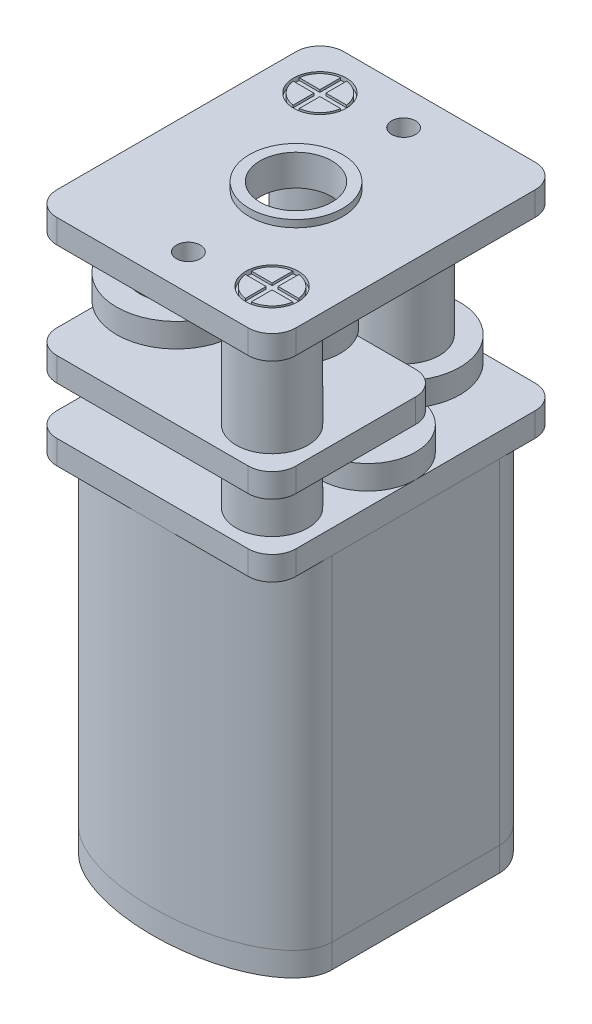
SolidWorks part; units mm, degrees
ref_plane "Alzado" through (0, 0, 0) normal (0, 0, 1) x (1, 0, 0)
ref_plane "Planta" through (0, 0, 0) normal (0, 1, 0) x (1, 0, 0)
ref_plane "Vista lateral" through (0, 0, 0) normal (1, 0, 0) x (0, 0, -1)
sketch "Croquis1" plane through (0, 0, 0) normal (0, 1, 0) x (1, 0, 0)
  line L0 (0, 0) -> (0, 3.5) construction
  line L1 (-5, -6) -> (5, -6) construction
  line L2 (-5, -6) -> (-5, 6) construction
  line L3 (-5, 6) -> (5, 6) construction
  line L4 (5, -6) -> (5, 6) construction
  line L5 (-5, -6) -> (5, 6) construction
  line L6 (-5, 6) -> (5, -6) construction
  line L7 (0, 0) -> (0, -3.5) construction
  line L8 (-5, 3.5) -> (0, 3.5) construction
  line L9 (0, 3.5) -> (5, 3.5) construction
  line L10 (-5, -3.5) -> (0, -3.5) construction
  line L11 (0, -3.5) -> (5, -3.5) construction
  line L12 (0, 0) -> (5, 0) construction
  line L13 (0, 0) -> (-5, 0) construction
  line L14 (5, 3.5) -> (5, -3.5)
  line L15 (-5, 3.5) -> (-5, -3.5)
  ellipse E0 centre (0, -3.5) end of major axis (5, -3.5) minor radius 2.5 (5, -3.5) -> (-5, -3.5) cw
  ellipse E1 centre (0, 3.5) end of major axis (-5, 3.5) minor radius 2.5 (5, 3.5) -> (-5, 3.5) ccw
  point P0 (0, 0)
  dimension "D1" = 12
  dimension "D2" = 10
extrude "Saliente-Extruir1" add sketch "Croquis1" along normal blind 1
sketch "Croquis2" plane through (0, 0, 0) normal (0, -1, 0) x (1, 0, 0)
  line L0 (-5, 3.5) -> (0, 3.5) construction
  line L1 (0, 3.5) -> (5, 3.5) construction
  line L2 (0, 0) -> (5, 0) construction
  line L3 (5, 3.5) -> (5, -3.5) construction
  line L4 (0, 0) -> (0, 3.5) construction
  line L5 (-5, -3.5) -> (0, -3.5) construction
  line L6 (0, -3.5) -> (5, -3.5) construction
  circle A0 centre (0, 0) radius 2.5
extrude "Saliente-Extruir2" add sketch "Croquis2" along normal blind 1
sketch "Croquis3" plane through (0, -1, 0) normal (0, -1, 0) x (1, 0, 0)
  circle A0 centre (0, 0) radius 1
extrude "Cortar-Extruir1" cut sketch "Croquis3" against normal blind 0.5
sketch "Croquis4" plane through (0, 0, 0) normal (0, -1, 0) x (1, 0, 0)
  line L0 (5, 3.5) -> (-5, 3.5) construction
  line L1 (-5, -3.5) -> (5, -3.5) construction
  line L2 (0, 0) -> (5, 0) construction
  line L4 (0, 0) -> (0, 3.5) construction
  line L5 (-0.75, 3.5) -> (0.75, 3.5)
  line L6 (0.75, 3.5) -> (0.75, 3.8)
  line L7 (-0.75, 3.5) -> (-0.75, 3.8)
  line L8 (-0.75, 3.8) -> (0.75, 3.8)
  line L9 (-0.75, -3.5) -> (-0.75, -3.8)
  line L10 (-0.75, -3.8) -> (0.75, -3.8)
  line L11 (0.75, -3.5) -> (0.75, -3.8)
  line L12 (-0.75, -3.5) -> (0.75, -3.5)
  line L13 (5, 3.5) -> (5, -3.5) construction
extrude "Saliente-Extruir3" add sketch "Croquis4" along normal blind 1.5
sketch "Croquis5" plane through (0, 0, -3.8) normal (0, 0, -1) x (-1, 0, 0)
  line L0 (0, -1.5) -> (0, 0) construction
  line L1 (0.75, -1.5) -> (-0.75, -1.5) construction
  line L2 (-0.75, -0.75) -> (0, -0.75) construction
  line L3 (-0.75, -1.5) -> (-0.75, 0) construction
  line L4 (0, -0.75) -> (0.75, -0.75) construction
  line L5 (0.75, -1.5) -> (0.75, 0) construction
  circle A0 centre (0, -0.75) radius 0.5
extrude "Cortar-Extruir2" cut sketch "Croquis5" against normal blind 0.3
sketch "Croquis6" plane through (0, 0, 3.8) normal (0, 0, 1) x (1, 0, 0)
  line L0 (0, -1.5) -> (0, 0) construction
  line L1 (0.75, -1.5) -> (-0.75, -1.5) construction
  line L2 (0.75, 0) -> (-0.75, 0) construction
  line L3 (0, -0.75) -> (0.75, -0.75) construction
  line L4 (0.75, -1.5) -> (0.75, 0) construction
  line L5 (0, -0.75) -> (-0.75, -0.75) construction
  line L6 (-0.75, -1.5) -> (-0.75, 0) construction
  circle A0 centre (0, -0.75) radius 0.5
extrude "Cortar-Extruir3" cut sketch "Croquis6" against normal blind 0.3
sketch "Croquis7" plane through (0, 1, 0) normal (0, 1, 0) x (1, 0, 0)
  line L2 (-5, 3.5) -> (-5, -3.5)
  line L3 (5, -3.5) -> (5, 3.5)
  line L4 (-5, 3.5) -> (-5, -3.5)
  line L5 (5, -3.5) -> (5, 3.5)
  ellipse E2 centre (0, 3.5) end of major axis (-5, 3.5) minor radius 2.5 (5, 3.5) -> (-5, 3.5) ccw
  ellipse E3 centre (0, -3.5) end of major axis (-5, -3.5) minor radius 2.5 (-5, -3.5) -> (5, -3.5) ccw
  ellipse E4 centre (0, 3.5) end of major axis (-5, 3.5) minor radius 2.5 (5, 3.5) -> (-5, 3.5) ccw
  ellipse E5 centre (0, -3.5) end of major axis (-5, -3.5) minor radius 2.5 (-5, -3.5) -> (5, -3.5) ccw
  dimension "D1" = 0
extrude "Saliente-Extruir4" add sketch "Croquis7" along normal blind 14 separate body
sketch "Croquis8" plane through (0, 15, 0) normal (0, 1, 0) x (1, 0, 0)
  line L1 (-5, 6) -> (5, 6)
  line L2 (5, 6) -> (5, -6)
  line L3 (5, -6) -> (-5, -6)
  line L4 (-5, -6) -> (-5, 6)
extrude "Saliente-Extruir5" add sketch "Croquis8" along normal blind 1 separate body
sketch "Croquis23" plane through (0, 16, 0) normal (0, 1, 0) x (1, 0, 0)
  line L0 (5, 6) -> (5, 1) construction
  line L1 (5, -6) -> (5, 6) construction
  line L2 (5, 6) -> (0, 6) construction
  line L3 (5, 6) -> (-5, 6) construction
  line L4 (0, 6) -> (0, 1) construction
  line L5 (0, 1) -> (5, 1) construction
  circle A0 centre (0, 0) radius 1
extrude "Saliente-Extruir13" add sketch "Croquis23" along normal blind 1 separate body
sketch "Croquis25" plane through (0, 16, 0) normal (0, 1, 0) x (1, 0, 0)
  line L0 (1, 0) -> (5, 0) construction
  line L1 (5, -6) -> (5, 6) construction
  circle A0 centre (0, 0) radius 1 construction
  circle A1 centre (3, 0) radius 2
extrude "Saliente-Extruir18" add sketch "Croquis25" along normal blind 1 separate body
sketch "Croquis26" plane through (0, 17, 0) normal (0, 1, 0) x (1, 0, 0)
  circle A0 centre (3, 0) radius 1
extrude "Saliente-Extruir19" add sketch "Croquis26" along normal blind 1
sketch "Croquis27" plane through (0, 17, 0) normal (0, 1, 0) x (1, 0, 0)
  line L0 (3, 1) -> (5, 1) construction
  line L1 (5, -6) -> (5, 6) construction
  line L2 (5, 1) -> (5, 6) construction
  line L3 (5, 6) -> (0, 6) construction
  line L4 (5, 6) -> (-5, 6) construction
  line L5 (0, 6) -> (0, 1) construction
  line L6 (0, 1) -> (3, 1) construction
  line L7 (1, 3) -> (2, 3) construction
  line L8 (1, 1) -> (1, 2) construction
  line L9 (1, 2) -> (0, 2) construction
  line L10 (2, 3) -> (2, 2) construction
  circle A0 centre (3, 0) radius 1 construction
  circle A1 centre (3, 0) radius 1 construction
  circle A2 centre (1, 2) radius 1 construction
  circle A3 centre (1.5, 3) radius 2.3541
extrude "Saliente-Extruir21" add sketch "Croquis27" along normal blind 1 separate body
sketch "Croquis29" plane through (0, 18, 0) normal (0, 1, 0) x (1, 0, 0)
  circle A0 centre (1.5, 3) radius 1.5
extrude "Saliente-Extruir22" add sketch "Croquis29" along normal blind 3
fillet "Redondeo1" radius 1 1 edges at (-5, 15.5, -6)
fillet "Redondeo2" radius 1 1 edges at (5, 15.5, -6)
fillet "Redondeo3" radius 1 1 edges at (5, 15.5, 6)
fillet "Redondeo4" radius 1 1 edges at (-5, 15.5, 6)
sketch "Croquis9" plane through (0, 16, 0) normal (0, 1, 0) x (1, 0, 0)
  line L0 (-5, 6) -> (-1, 6) construction
  line L1 (-3, 2) -> (-3, 6) construction
  line L2 (4, 6) -> (-4, 6) construction
  line L3 (-1, 6) -> (-1, 2) construction
  line L4 (-1, 2) -> (-5, 2) construction
  line L5 (-5, 5) -> (-5, -5) construction
  line L6 (-5, 2) -> (-5, 6) construction
  line L7 (-5, 4) -> (-3, 4) construction
  line L8 (-3, 4) -> (-1, 4) construction
  line L9 (5, -6) -> (1, -6) construction
  line L10 (-4, -6) -> (4, -6) construction
  line L11 (1, -6) -> (1, -2) construction
  line L12 (1, -2) -> (5, -2) construction
  line L13 (5, -5) -> (5, 5) construction
  line L14 (5, -2) -> (5, -6) construction
  line L15 (3, -2) -> (3, -6) construction
  line L16 (1, -4) -> (3, -4) construction
  line L17 (3, -4) -> (5, -4) construction
  circle A0 centre (-3, 4) radius 1.5
  circle A1 centre (3, -4) radius 1.5
extrude "Saliente-Extruir6" add sketch "Croquis9" along normal blind 2
sketch "Croquis10" plane through (0, 18, 0) normal (0, 1, 0) x (1, 0, 0)
  line L0 (-3, 4) -> (-5, 4) construction
  line L1 (-5, 5) -> (-5, -5) construction
  line L2 (-3, 4) -> (-3, 6) construction
  line L3 (4, 6) -> (-4, 6) construction
  line L4 (-5, 6) -> (5, 6)
  line L5 (5, 6) -> (5, -6)
  line L6 (5, -6) -> (-5, -6)
  line L7 (-5, -6) -> (-5, 6)
extrude "Saliente-Extruir7" add sketch "Croquis10" along normal blind 1
sketch "Croquis11" plane through (0, 19, 0) normal (0, 1, 0) x (1, 0, 0)
  line L0 (5, -6) -> (3, -6) construction
  line L1 (-5, -6) -> (5, -6) construction
  line L2 (3, -6) -> (3, -4) construction
  line L3 (3, -4) -> (5, -4) construction
  line L4 (5, -6) -> (5, 6) construction
  line L5 (5, -4) -> (5, -6) construction
  line L6 (-5, 6) -> (-5, 4) construction
  line L7 (-5, 6) -> (-5, -6) construction
  line L8 (-5, 4) -> (-3, 4) construction
  line L9 (-3, 4) -> (-3, 6) construction
  line L10 (5, 6) -> (-5, 6) construction
  line L11 (-3, 6) -> (-5, 6) construction
  circle A0 centre (3, -4) radius 1.5
  circle A1 centre (-3, 4) radius 1.5
extrude "Saliente-Extruir8" add sketch "Croquis11" along normal blind 4
sketch "Croquis12" plane through (0, 19, 0) normal (0, 1, 0) x (1, 0, 0)
  line L0 (5, 6) -> (0, 6)
  line L1 (5, 6) -> (-5, 6) construction
  line L2 (0, 6) -> (0, 1)
  line L3 (0, 1) -> (5, 1)
  line L4 (5, -6) -> (5, 6) construction
  line L5 (5, 1) -> (5, 6)
extrude "Cortar-Extruir4" cut sketch "Croquis12" against normal blind 1
sketch "Croquis30" plane through (0, 19, 0) normal (0, 1, 0) x (1, 0, 0)
  circle A0 centre (0, 0) radius 1.8541
extrude "Saliente-Extruir24" add sketch "Croquis30" along normal blind 1 separate body
sketch "Croquis31" plane through (0, 20, 0) normal (0, 1, 0) x (1, 0, 0)
  circle A0 centre (0, 0) radius 1
extrude "Saliente-Extruir26" add sketch "Croquis31" along normal blind 1 separate body
sketch "Croquis32" plane through (0, 20, 0) normal (0, 1, 0) x (1, 0, 0)
  line L0 (0, 0) -> (0, -2) construction
  line L1 (0, -2) -> (-2, -2) construction
  line L2 (-2, -2) -> (-2, 0) construction
  line L3 (-2, 0) -> (-3, 0) construction
  line L4 (-3, 0) -> (-3, -3) construction
  line L5 (-3, -3) -> (0, -3) construction
  line L6 (0, -3) -> (0, -2) construction
  line L7 (-2.5, 0) -> (-2.5, -2.5) construction
  line L8 (-2.5, -2.5) -> (0, -2.5) construction
  circle A0 centre (0, 0) radius 2 construction
  circle A1 centre (-2.5, -2.5) radius 2.5
extrude "Saliente-Extruir27" add sketch "Croquis32" along normal blind 1 separate body
sketch "Croquis33" plane through (0, 21, 0) normal (0, 1, 0) x (1, 0, 0)
  circle A0 centre (0, 0) radius 2 construction
  circle A1 centre (-2.5, -2.5) radius 1.5355
extrude "Saliente-Extruir28" add sketch "Croquis33" along normal blind 2 separate body
sketch "Croquis34" plane through (0, 21, 0) normal (0, 1, 0) x (1, 0, 0)
  circle A0 centre (1.5, 3) radius 0.2
extrude "Saliente-Extruir29" add sketch "Croquis34" along normal blind 2 and the other way blind 5 separate body
sketch "Croquis35" plane through (0, 23, 0) normal (0, 1, 0) x (1, 0, 0)
  circle A0 centre (-2.5, -2.5) radius 0.2
extrude "Saliente-Extruir30" add sketch "Croquis35" against normal blind 4 separate body
sketch "Croquis36" plane through (0, 21, 0) normal (0, 1, 0) x (1, 0, 0)
  circle A0 centre (0, 0) radius 0.2
extrude "Saliente-Extruir31" add sketch "Croquis36" along normal blind 2 separate body
fillet "Redondeo5" radius 1 1 edges at (5, 18.5, -1)
fillet "Redondeo6" radius 1 1 edges at (0, 18.5, -6)
fillet "Redondeo7" radius 1 1 edges at (-5, 18.5, -6)
fillet "Redondeo8" radius 1 1 edges at (-5, 18.5, 6)
fillet "Redondeo9" radius 1 1 edges at (5, 18.5, 6)
sketch "Croquis13" plane through (0, 23, 0) normal (0, 1, 0) x (1, 0, 0)
  line L2 (-5, 6) -> (5, 6)
  line L3 (5, 6) -> (5, -6)
  line L4 (5, -6) -> (-5, -6)
  line L5 (-5, -6) -> (-5, 6)
extrude "Saliente-Extruir9" add sketch "Croquis13" along normal blind 1
sketch "Croquis14" plane through (0, 24, 0) normal (0, 1, 0) x (1, 0, 0)
  line L0 (0, 6) -> (0, 0) construction
  line L1 (5, 6) -> (-5, 6) construction
  line L2 (0, 0) -> (0, -6) construction
  line L3 (-5, -6) -> (5, -6) construction
  line L4 (-5, 0) -> (0, 0) construction
  line L5 (-5, 6) -> (-5, -6) construction
  line L6 (0, 0) -> (5, 0) construction
  circle A0 centre (0, 0) radius 1.95
  circle A1 centre (0, 0) radius 1.5
extrude "Saliente-Extruir10" add sketch "Croquis14" along normal blind 0.3
sketch "Croquis15" plane through (0, 24, 0) normal (0, 1, 0) x (1, 0, 0)
  line L0 (0, 0) -> (0, 4.5) construction
  line L1 (0, 0) -> (5, 0) construction
  circle A0 centre (0, 4.5) radius 0.5
  circle A1 centre (0, -4.5) radius 0.5
extrude "Cortar-Extruir5" cut sketch "Croquis15" against normal blind 1
sketch "Croquis16" plane through (0, 24, 0) normal (0, 1, 0) x (1, 0, 0)
  line L0 (5, -6) -> (5, -4) construction
  line L1 (5, -6) -> (5, 6) construction
  line L2 (5, -4) -> (3, -4) construction
  line L3 (3, -4) -> (3, -6) construction
  line L4 (-5, -6) -> (5, -6) construction
  line L5 (3, -6) -> (5, -6) construction
  line L6 (-5, 6) -> (-3, 6) construction
  line L7 (5, 6) -> (-5, 6) construction
  line L8 (-3, 6) -> (-3, 4) construction
  line L9 (-3, 4) -> (-5, 4) construction
  line L10 (-5, 6) -> (-5, -6) construction
  line L11 (-5, 4) -> (-5, 6) construction
  circle A0 centre (3, -4) radius 1.1
  circle A1 centre (-3, 4) radius 1.1
extrude "Cortar-Extruir6" cut sketch "Croquis16" against normal blind 0.2
sketch "Croquis17" plane through (0, 23.8, 0) normal (0, 1, 0) x (1, 0, 0)
  circle A0 centre (-3, 4) radius 1
extrude "Saliente-Extruir11" add sketch "Croquis17" along normal blind 0.2 separate body
sketch "Croquis18" plane through (0, 23.8, 0) normal (0, 1, 0) x (1, 0, 0)
  circle A0 centre (3, -4) radius 1
extrude "Saliente-Extruir12" add sketch "Croquis18" along normal blind 0.2 separate body
sketch "Croquis19" plane through (0, 24, 0) normal (0, 1, 0) x (1, 0, 0)
  line L0 (-3, 4) -> (-3, 5) construction
  line L1 (-3, 4) -> (-3, 3) construction
  line L2 (-3, 4) -> (-2, 4) construction
  line L3 (-3, 4) -> (-4, 4) construction
  line L4 (-3.125, 4.125) -> (-3.125, 4.9922)
  line L5 (-3.125, 3.875) -> (-2.875, 3.875) construction
  line L6 (-3.125, 3.875) -> (-3.125, 4.125) construction
  line L7 (-3.125, 4.125) -> (-2.875, 4.125) construction
  line L8 (-2.875, 3.875) -> (-2.875, 4.125) construction
  line L9 (-3.125, 3.875) -> (-2.875, 4.125) construction
  line L10 (-3.125, 4.125) -> (-2.875, 3.875) construction
  line L11 (-2.875, 4.125) -> (-2.875, 4.9922)
  line L12 (-2.875, 4.125) -> (-2.0078, 4.125)
  line L13 (-2.875, 3.875) -> (-2.0078, 3.875)
  line L14 (-2.875, 3.875) -> (-2.875, 3.0078)
  line L15 (-3.125, 3.875) -> (-3.125, 3.0078)
  line L16 (-3.125, 3.875) -> (-3.9922, 3.875)
  line L17 (-3.125, 4.125) -> (-3.9922, 4.125)
  circle A0 centre (-3, 4) radius 1 construction
  arc A1 (-3.9922, 4.125) -> (-3.9922, 3.875) centre (-3, 4) ccw
  arc A2 (-2.875, 4.9922) -> (-3.125, 4.9922) centre (-3, 4) ccw
  arc A3 (-2.0078, 3.875) -> (-2.0078, 4.125) centre (-3, 4) ccw
  arc A4 (-3.125, 3.0078) -> (-2.875, 3.0078) centre (-3, 4) ccw
  dimension "D1" = 0.25
  dimension "D2" = 0.25
extrude "Cortar-Extruir7" cut sketch "Croquis19" against normal blind 0.1
sketch "Croquis21" plane through (0, 24, 0) normal (0, 1, 0) x (1, 0, 0)
  line L0 (3, -4) -> (3, -3) construction
  line L1 (3, -4) -> (4, -4) construction
  line L2 (3, -4) -> (3, -5) construction
  line L3 (3, -4) -> (2, -4) construction
  line L4 (2.875, -3.875) -> (2.875, -3.0078)
  line L5 (2.875, -4.125) -> (3.125, -4.125) construction
  line L6 (2.875, -4.125) -> (2.875, -3.875) construction
  line L7 (2.875, -3.875) -> (3.125, -3.875) construction
  line L8 (3.125, -4.125) -> (3.125, -3.875) construction
  line L9 (2.875, -4.125) -> (3.125, -3.875) construction
  line L10 (2.875, -3.875) -> (3.125, -4.125) construction
  line L11 (3.125, -3.875) -> (3.125, -3.0078)
  line L12 (3.125, -3.875) -> (3.9922, -3.875)
  line L13 (3.125, -4.125) -> (3.9922, -4.125)
  line L14 (3.125, -4.125) -> (3.125, -4.9922)
  line L15 (2.875, -4.125) -> (2.875, -4.9922)
  line L16 (2.875, -4.125) -> (2.0078, -4.125)
  line L17 (2.875, -3.875) -> (2.0078, -3.875)
  circle A0 centre (3, -4) radius 1 construction
  arc A1 (2.0078, -3.875) -> (2.0078, -4.125) centre (3, -4) ccw
  arc A2 (3.125, -3.0078) -> (2.875, -3.0078) centre (3, -4) ccw
  arc A3 (3.9922, -4.125) -> (3.9922, -3.875) centre (3, -4) ccw
  arc A4 (2.875, -4.9922) -> (3.125, -4.9922) centre (3, -4) ccw
  dimension "D1" = 0.25
  dimension "D2" = 0.25
extrude "Cortar-Extruir8" cut sketch "Croquis21" against normal blind 0.1
fillet "Redondeo10" radius 1 1 edges at (-5, 23.5, 6)
fillet "Redondeo11" radius 1 1 edges at (5, 23.5, 6)
fillet "Redondeo12" radius 1 1 edges at (5, 23.5, -6)
fillet "Redondeo13" radius 1 1 edges at (-5, 23.5, -6)
fillet "Redondeo14" radius 1 1 edges at (0, 18.5, -1)
sketch "Croquis22" plane through (0, 24, 0) normal (0, 1, 0) x (1, 0, 0)
  line L0 (0, 0) -> (1.5, 0) construction
  circle A1 centre (0, 0) radius 1.5
  circle A2 centre (0, 0) radius 1.5
  dimension "D1" = 0
extrude "Cortar-Extruir9" cut sketch "Croquis22" against normal blind 1
